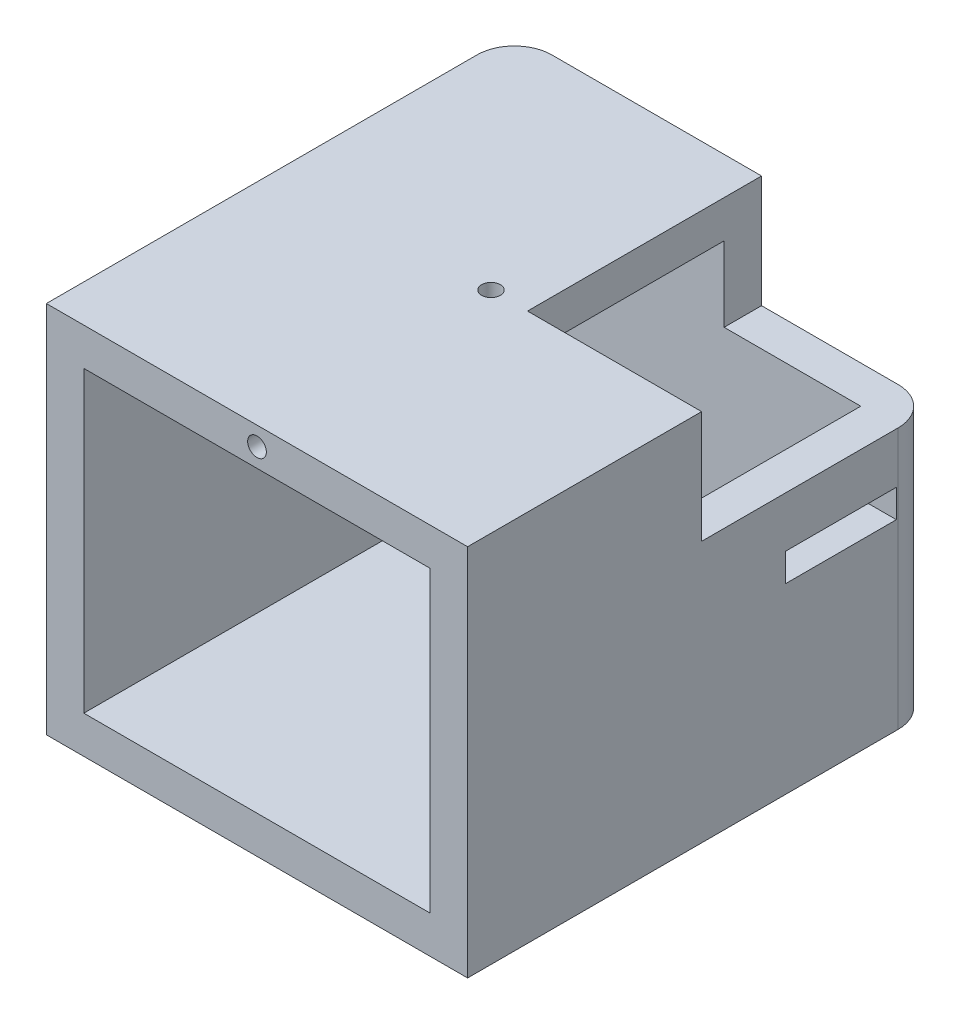
SolidWorks part; units mm, degrees
ref_plane "Alzado" through (0, 0, 0) normal (0, 0, 1) x (1, 0, 0)
ref_plane "Planta" through (0, 0, 0) normal (0, 1, 0) x (1, 0, 0)
ref_plane "Vista lateral" through (0, 0, 0) normal (1, 0, 0) x (0, 0, -1)
sketch "Croquis1" plane through (0, 0, 0) normal (1, 0, 0) x (0, 0, -1)
  line L0 (-5.9, 11.75) -> (5.9, 11.75) construction
  line L1 (5.9, 11.75) -> (5.9, -14.95) construction
  line L2 (5.9, -14.95) -> (-5.9, -14.95) construction
  line L3 (-5.9, -14.95) -> (-5.9, 11.75) construction
  line L4 (-2.3, 11.75) -> (-2.3, 14.95) construction
  line L5 (-2.3, 14.95) -> (2.3, 14.95) construction
  line L6 (2.3, 14.95) -> (2.3, 11.75) construction
  line L8 (25, 19.95) -> (-25, 19.95)
  line L9 (25, 19.95) -> (25, -19.95)
  line L10 (25, -19.95) -> (-25, -19.95)
  line L11 (-25, 19.95) -> (-25, -19.95)
  point P6 (0, 14.95)
  point P9 (0, 19.95)
  point P10 (25, 0)
  point P19 (0, -14.95)
  dimension "D1" = 11.8
  dimension "D2" = 26.7
  dimension "D3" = 3.6
  dimension "D4" = 5.9
  dimension "D5" = 3.2
  dimension "D6" = 50
  dimension "D7" = 5
  dimension "D8" = 5
extrude "Saliente-Extruir1" add sketch "Croquis1" along normal mid plane 45
shell "Vaciado1" thickness 4
sketch "Croquis2" plane through (0, 19.95, 0) normal (0, 1, 0) x (1, 0, 0)
  line L0 (-22.5, 0) -> (-18.5, 0) construction
  line L1 (-22.5, 25) -> (-22.5, -25) construction
  line L2 (-18.5, 0) -> (-13.8, 0) construction
  line L3 (-13.8, 0) -> (8.7, 0) construction
  line L4 (8.7, 0) -> (13.4, 0) construction
  line L5 (22.5, 25) -> (22.5, -25) construction
  line L6 (22.5, 0) -> (18.5, 0) construction
  line L7 (-13.8, 0) -> (-7.9, 0) construction
  line L8 (-22.5, 25) -> (-5.9, 25)
  line L9 (22.5, 25) -> (-22.5, 25) construction
  line L10 (-5.9, 25) -> (-5.9, 21)
  line L11 (-5.9, 21) -> (-18.5, 21)
  line L12 (-18.5, 21) -> (-18.5, 0)
  line L13 (-18.5, 0) -> (-22.5, 0)
  line L14 (-22.5, 0) -> (-22.5, 25)
  line L15 (0, -21.945) -> (0, 21.945) construction
  line L16 (18.5, 0) -> (22.5, 0)
  line L17 (18.5, 21) -> (18.5, 0)
  line L18 (5.9, 21) -> (18.5, 21)
  line L19 (5.9, 25) -> (5.9, 21)
  line L20 (22.5, 25) -> (5.9, 25)
  line L21 (22.5, 0) -> (22.5, 25)
  dimension "D2" = 4.7
  dimension "D3" = 22.5
  dimension "D4" = 4.7
  dimension "D5" = 5.9
  dimension "D6" = 2
  dimension "D7" = 4
  dimension "D8" = 4
extrude "Cortar-Extruir1" cut sketch "Croquis2" along normal blind 3.5 from offset 9.2 offset against normal yes
sketch "Croquis4" plane through (0, 19.95, 0) normal (0, 1, 0) x (1, 0, 0)
  circle A0 centre (0, 0) radius 1
  dimension "D1" = 2
extrude "Cortar-Extruir3" cut sketch "Croquis4" against normal up to next and the other way through all
sketch "Croquis5" plane through (0, 0, 25) normal (0, 0, 1) x (1, 0, 0)
  line L0 (0, 18.95) -> (0, 19.95) construction
  line L3 (0, 16.95) -> (0, 15.95) construction
  line L5 (18.5, 15.95) -> (-18.5, 15.95) construction
  line L6 (0, 19.95) -> (0, -19.95) construction
  line L7 (22.5, 19.95) -> (-22.5, 19.95) construction
  circle A0 centre (0, 17.95) radius 1
  dimension "D1" = 2
extrude "Cortar-Extruir4" cut sketch "Croquis5" against normal blind 5
sketch "Croquis6" plane through (-22.5, 0, 0) normal (-1, 0, 0) x (0, 0, 1)
  line L1 (14.9154, -2.254) -> (21.0373, -2.254)
  line L2 (14.9154, -2.254) -> (14.9154, -16.5015)
  line L3 (14.9154, -16.5015) -> (21.0373, -16.5015)
  line L4 (21.0373, -2.254) -> (21.0373, -16.5015)
sketch "Croquis7" plane through (0, 19.95, 0) normal (0, 1, 0) x (1, 0, 0)
  line L0 (5.9, 21) -> (5.9, 0) construction
  line L1 (5.9, 0) -> (18.5, 0)
  line L2 (5.9, 25) -> (3.9, 25)
  line L3 (22.5, 25) -> (-22.5, 25) construction
  line L4 (3.9, 25) -> (3.9, 0)
  line L5 (3.9, 0) -> (5.9, 0)
  line L6 (22.5, 0) -> (22.5, 25)
  line L7 (22.5, 25) -> (5.9, 25)
  line L8 (5.9, 25) -> (5.9, 21)
  line L9 (5.9, 21) -> (18.5, 21)
  line L10 (18.5, 21) -> (18.5, 0)
  line L11 (18.5, 0) -> (22.5, 0)
  line L12 (22.5, 0) -> (22.5, 25)
  line L13 (22.5, 25) -> (5.9, 25)
  line L14 (5.9, 25) -> (5.9, 21) construction
  line L15 (5.9, 21) -> (18.5, 21) construction
  line L16 (18.5, 21) -> (18.5, 0) construction
  line L17 (18.5, 0) -> (22.5, 0)
  dimension "D2" = 2
  dimension "D1" = 0
extrude "Cortar-Extruir5" cut sketch "Croquis7" against normal blind 12
sketch "Croquis8" plane through (-22.5, 0, 0) normal (-1, 0, 0) x (0, 0, 1)
  line L0 (25, -19.95) -> (-25, -19.95) construction
  line L1 (-20.8, 2.55) -> (-8.95, 2.55)
  line L2 (-20.8, 2.55) -> (-20.8, -0.45)
  line L3 (-20.8, -0.45) -> (-8.95, -0.45)
  line L4 (-8.95, 2.55) -> (-8.95, -0.45)
  line L5 (-25, -19.95) -> (-25, 10.75) construction
  dimension "D1" = 19.5
  dimension "3" = 3
  dimension "D3" = 11.85
  dimension "D4" = 4.2
extrude "Cortar-Extruir6" cut sketch "Croquis8" against normal through all both and the other way through all
fillet "Redondeo1" radius 4 3 edges at (22.5, -6, -25) (-22.5, -4.6, -25) (-22.5, 17.1, -25)
